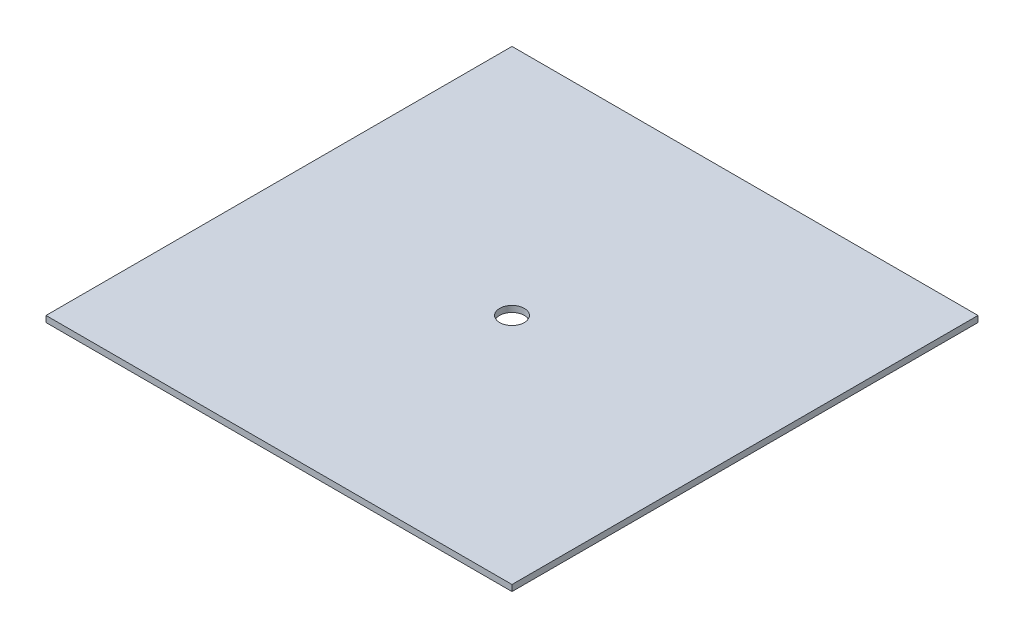
SolidWorks part; units mm, degrees
material "PTFE (general)"
ref_plane "Front Plane" through (0, 0, 0) normal (0, 0, 1) x (1, 0, 0)
ref_plane "Top Plane" through (0, 0, 0) normal (0, 1, 0) x (1, 0, 0)
ref_plane "Right Plane" through (0, 0, 0) normal (1, 0, 0) x (0, 0, -1)
sketch "Sketch1" plane through (0, 0, 0) normal (0, 1, 0) x (1, 0, 0)
  line L12 (17.5573, 30.5402) -> (17.5573, -29.4598)
  line L13 (17.5573, -29.4598) -> (77.5573, -29.4598)
  line L14 (77.5573, -29.4598) -> (77.5573, 30.5402)
  line L16 (17.5573, 30.5402) -> (77.5573, 30.5402)
  circle A3 centre (47.5573, 0.5402) radius 1.5875
  dimension "D1" = 3.175
extrude "Boss-Extrude1" add sketch "Sketch1" along normal blind 0.7937
